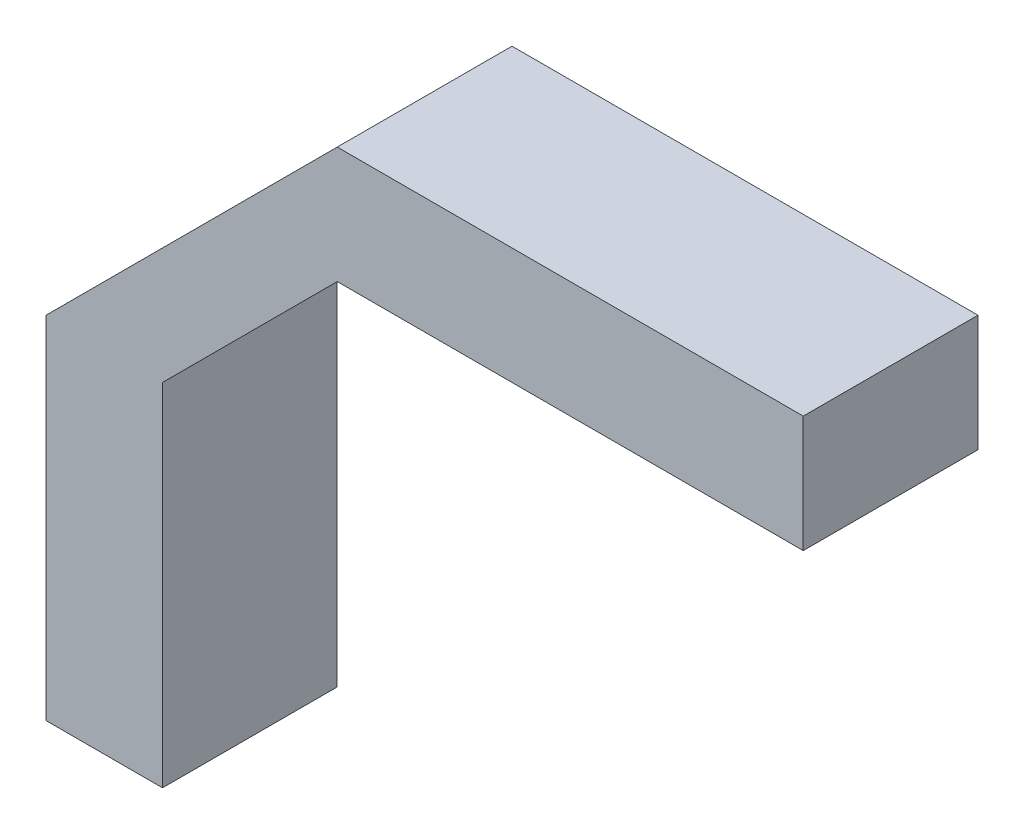
SolidWorks part; units mm, degrees
ref_plane "Front Plane" through (0, 0, 0) normal (0, 0, 1) x (1, 0, 0)
ref_plane "Top Plane" through (0, 0, 0) normal (0, 1, 0) x (1, 0, 0)
ref_plane "Right Plane" through (0, 0, 0) normal (1, 0, 0) x (0, 0, -1)
sketch "Sketch1" plane through (0, 0, 0) normal (0, 0, 1) x (1, 0, 0)
  line L6 (0, 0) -> (10, 0)
  line L10 (65, 55.1335) -> (25, 55.1335)
  line L11 (0, 0) -> (0, 30.1335)
  line L12 (0, 30.1335) -> (25, 55.1335)
  line L13 (10, 0) -> (10, 30.1335)
  line L14 (10, 30.1335) -> (25, 45.1335)
  line L15 (25, 45.1335) -> (65, 45.1335)
  line L16 (65, 55.1335) -> (65, 45.1335)
  line L17 (65, 55.1335) -> (65, 50.1335) construction
  dimension "D1" = 25
  dimension "D2" = 10
extrude "Boss-Extrude1" add sketch "Sketch1" along normal mid plane 15
